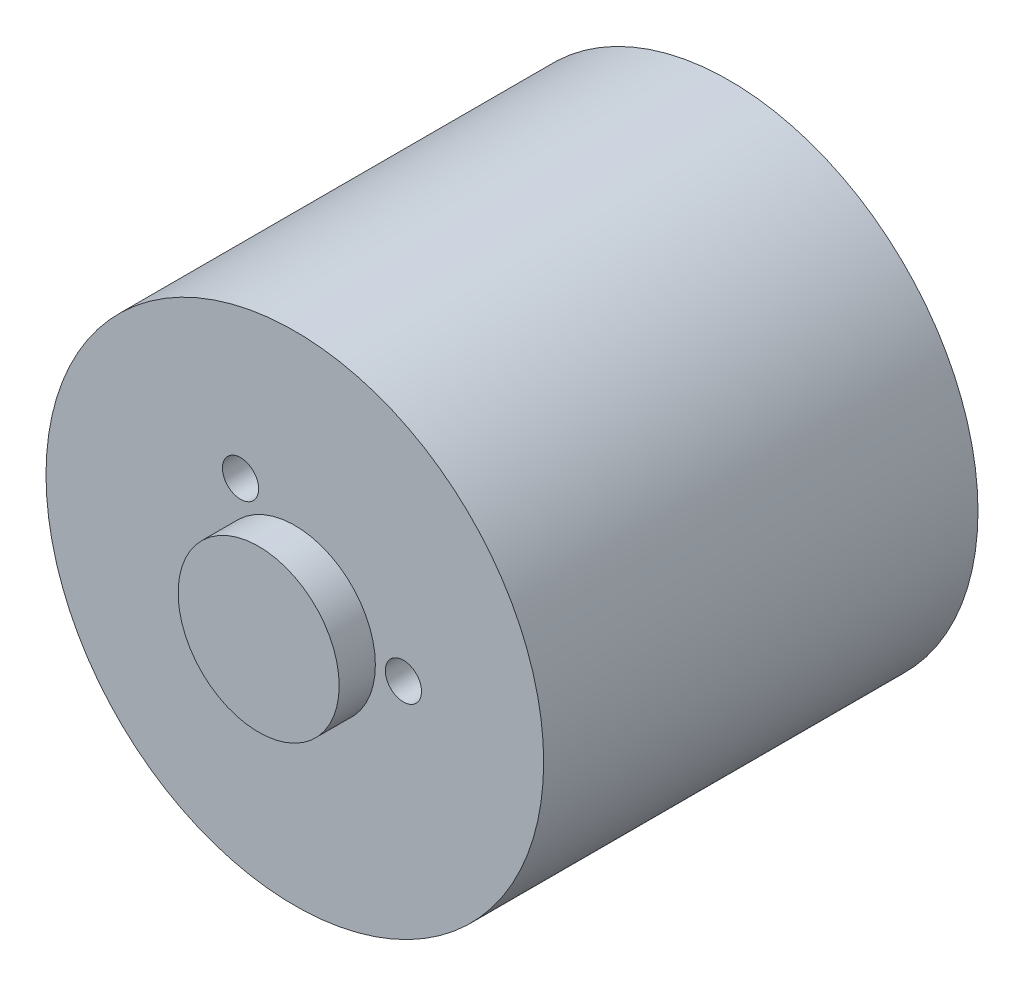
SolidWorks part; units mm, degrees
ref_plane "前视基准面" through (0, 0, 0) normal (0, 0, 1) x (1, 0, 0)
ref_plane "上视基准面" through (0, 0, 0) normal (0, 1, 0) x (1, 0, 0)
ref_plane "右视基准面" through (0, 0, 0) normal (1, 0, 0) x (0, 0, -1)
sketch "草图1" plane through (0, 0, 0) normal (0, 0, 1) x (1, 0, 0)
  circle A0 centre (0, 0) radius 13.75
extrude "凸台-拉伸1" add sketch "草图1" along normal blind 24
sketch "草图2" plane through (0, 0, 24) normal (0, 0, 1) x (1, 0, 0)
  circle A0 centre (0, 0) radius 4.45
extrude "凸台-拉伸2" add sketch "草图2" along normal blind 2
sketch "草图3" plane through (0, 0, 26) normal (0, 0, 1) x (1, 0, 0)
  line L0 (0, 0) -> (6, 0)
  circle A0 centre (6, 0) radius 1
  circle A1 centre (-3, -5.1962) radius 1
  circle A2 centre (-3, 5.1962) radius 1
  point P10 (0, 0)
  dimension "D1" = 3
extrude "切除-拉伸1" cut sketch "草图3" against normal blind 6
